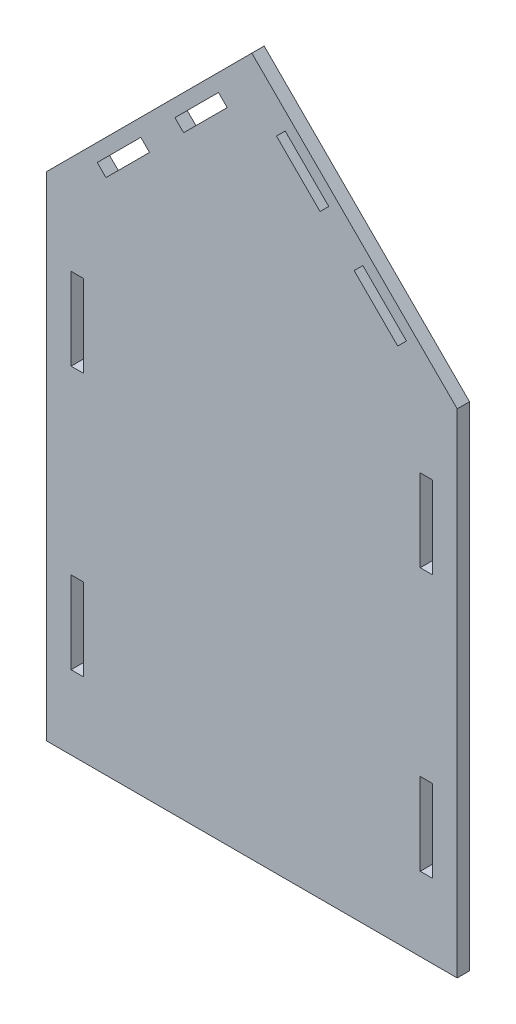
SolidWorks part; units mm, degrees
ref_plane "Alzado" through (0, 0, 0) normal (0, 0, 1) x (1, 0, 0)
ref_plane "Planta" through (0, 0, 0) normal (0, 1, 0) x (1, 0, 0)
ref_plane "Vista lateral" through (0, 0, 0) normal (1, 0, 0) x (0, 0, -1)
sketch "Sketch1" plane through (0, 0, 0) normal (0, 0, 1) x (1, 0, 0)
  line L0 (0, 0) -> (0, 600)
  line L1 (0, 600) -> (250, 850)
  line L2 (250, 850) -> (500, 600)
  line L3 (500, 600) -> (500, 0)
  line L4 (500, 0) -> (0, 0)
  line L5 (30, 510) -> (30, 410)
  line L6 (30, 410) -> (45, 410)
  line L7 (45, 410) -> (45, 510)
  line L8 (45, 510) -> (30, 510)
  line L9 (-576.938, 300) -> (1685.0052, 300) construction
  line L10 (250, 1232.9941) -> (250, -148.524) construction
  line L11 (455, 410) -> (455, 510)
  line L12 (470, 410) -> (455, 410)
  line L13 (470, 510) -> (470, 410)
  line L14 (455, 510) -> (470, 510)
  line L15 (470, 190) -> (455, 190)
  line L16 (470, 90) -> (470, 190)
  line L17 (455, 90) -> (470, 90)
  line L18 (455, 190) -> (455, 90)
  line L19 (45, 190) -> (45, 90)
  line L20 (30, 190) -> (45, 190)
  line L21 (30, 90) -> (30, 190)
  line L22 (45, 90) -> (30, 90)
  line L31 (61.8198, 640.6066) -> (72.4264, 630)
  line L32 (72.4264, 630) -> (125.4594, 683.033)
  line L33 (125.4594, 683.033) -> (114.8528, 693.6396)
  line L34 (114.8528, 693.6396) -> (61.8198, 640.6066)
  line L35 (-576.3641, 600) -> (805.1908, 600) construction
  line L36 (250, 600) -> (-38.2689, 888.2689) construction
  line L37 (166.967, 724.5406) -> (156.3604, 735.1472)
  line L38 (220, 777.5736) -> (166.967, 724.5406)
  line L39 (209.3934, 788.1802) -> (220, 777.5736)
  line L40 (156.3604, 735.1472) -> (209.3934, 788.1802)
  line L41 (280, 777.5736) -> (333.033, 724.5406)
  line L42 (290.6066, 788.1802) -> (280, 777.5736)
  line L43 (343.6396, 735.1472) -> (290.6066, 788.1802)
  line L44 (333.033, 724.5406) -> (343.6396, 735.1472)
  line L45 (374.5406, 683.033) -> (385.1472, 693.6396)
  line L46 (427.5736, 630) -> (374.5406, 683.033)
  line L47 (438.1802, 640.6066) -> (427.5736, 630)
  line L48 (385.1472, 693.6396) -> (438.1802, 640.6066)
  dimension "D1" = 250
  dimension "D2" = 500
  dimension "D3" = 850
  dimension "D4" = 30
  dimension "D5" = 15
  dimension "D6" = 100
  dimension "D7" = 90
  dimension "D8" = 300
  dimension "D13" = 15
  dimension "D14" = 75
  dimension "D15" = 15
  dimension "D16" = 30
  dimension "D17" = 45
extrude "Boss-Extrude1" add sketch "Sketch1" along normal blind 15 contours L4 L3 L2 L1 L0 L18 L15 L16 L17 L8 L7 L6 L5 L11 L14 L13 L12 L19 L22 L21 L20
